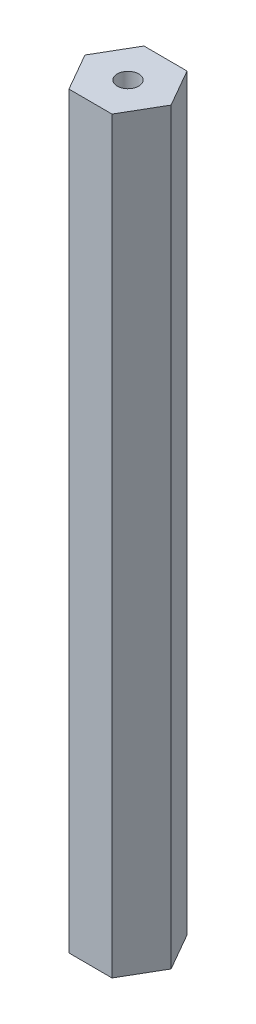
SolidWorks part; units mm, degrees
ref_plane "Front Plane" through (0, 0, 0) normal (0, 0, 1) x (1, 0, 0)
ref_plane "Top Plane" through (0, 0, 0) normal (0, 1, 0) x (1, 0, 0)
ref_plane "Right Plane" through (0, 0, 0) normal (1, 0, 0) x (0, 0, -1)
sketch "Sketch1" plane through (0, 0, 0) normal (0, 1, 0) x (1, 0, 0)
  line L1 (2.552, -4.4532) -> (5.1326, -0.0165)
  line L2 (5.1326, -0.0165) -> (2.5806, 4.4367)
  line L3 (2.5806, 4.4367) -> (-2.552, 4.4532)
  line L4 (-2.552, 4.4532) -> (-5.1326, 0.0165)
  line L5 (-5.1326, 0.0165) -> (-2.5806, -4.4367)
  line L6 (-2.5806, -4.4367) -> (2.552, -4.4532)
  circle A0 centre (0, 0) radius 4.445 construction
  circle A1 centre (0, 0) radius 1.27
  dimension "D1" = 8.89
  dimension "D2" = 2.54
extrude "Boss-Extrude1" add sketch "Sketch1" along normal blind 88.9
